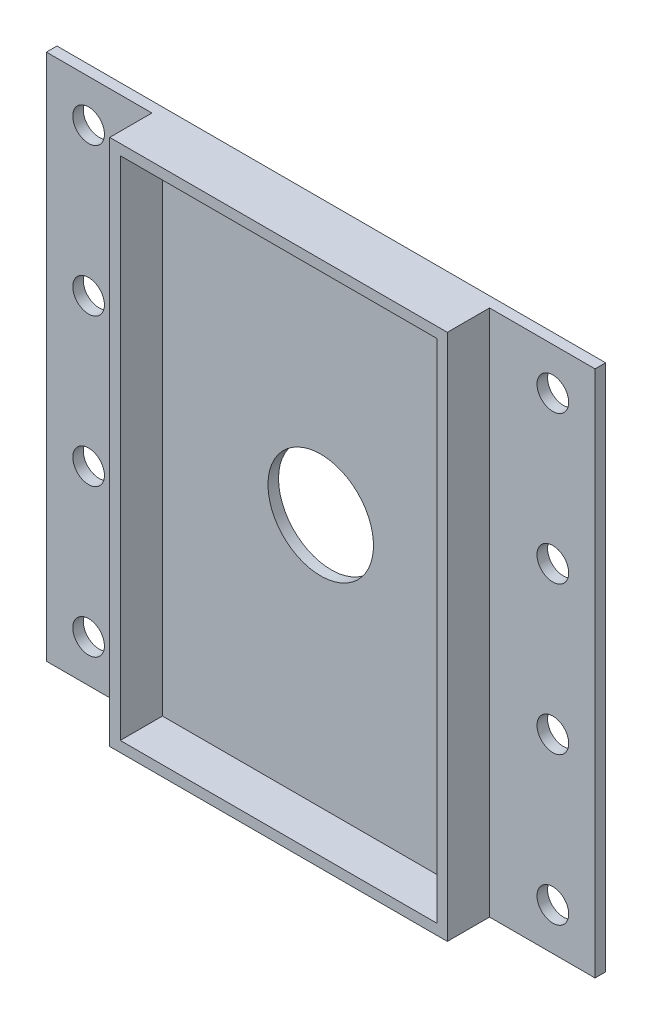
SolidWorks part; units mm, degrees
ref_plane "Plan de face" through (0, 0, 0) normal (0, 0, 1) x (1, 0, 0)
ref_plane "Plan de dessus" through (0, 0, 0) normal (0, 1, 0) x (1, 0, 0)
ref_plane "Plan de droite" through (0, 0, 0) normal (1, 0, 0) x (0, 0, -1)
sketch "Esquisse1" plane through (0, 0, 0) normal (0, 0, 1) x (1, 0, 0)
  line L0 (-5, 5) -> (-155, 5)
  line L1 (0, 0) -> (-160, 0)
  line L2 (0, 0) -> (0, 250)
  line L3 (0, 250) -> (-160, 250)
  line L4 (-160, 0) -> (-160, 250)
  line L5 (-155, 5) -> (-155, 245)
  line L6 (-5, 245) -> (-155, 245)
  line L7 (-5, 5) -> (-5, 245)
  dimension "D1" = 160
  dimension "D2" = 250
  dimension "D3" = 5
extrude "Boss.-Extru.1" add sketch "Esquisse1" along normal blind 20
sketch "Esquisse2" plane through (0, 0, 0) normal (0, 0, -1) x (-1, 0, 0)
  line L0 (155, 5) -> (5, 5) construction
  line L1 (-50, 250) -> (210, 250)
  line L2 (-50, 250) -> (-50, 0)
  line L3 (-50, 0) -> (210, 0)
  line L4 (210, 250) -> (210, 0)
  point P4 (80, 5)
  dimension "D1" = 260
  dimension "D2" = 130
extrude "Boss.-Extru.2" add sketch "Esquisse2" along normal blind 5
sketch "Esquisse3" plane through (0, 0, -5) normal (0, 0, -1) x (-1, 0, 0)
  line L0 (-50, 250) -> (210, 0) construction
  circle A0 centre (80, 125) radius 25
  dimension "D1" = 50
extrude "Enlèv. mat.-Extru.1" cut sketch "Esquisse3" against normal blind 5
sketch "Esquisse4" plane through (0, 0, 0) normal (0, 0, 1) x (1, 0, 0)
  line L0 (-210, 250) -> (-160, 250) construction
  line L1 (-210, 0) -> (-210, 250) construction
  line L2 (0, 250) -> (50, 250) construction
  line L4 (50, 250) -> (50, 0) construction
  circle A0 centre (30, 230) radius 7.5
  circle A1 centre (-190, 230) radius 7.5
  circle A2 centre (-190, 160) radius 7.5
  circle A3 centre (30, 160) radius 7.5
  circle A4 centre (-190, 90) radius 7.5
  circle A5 centre (30, 90) radius 7.5
  circle A6 centre (-190, 20) radius 7.5
  circle A7 centre (30, 20) radius 7.5
  point P4 (-185, 250)
  dimension "D6" = 15
  dimension "D7" = 15
  dimension "D1" = 20
  dimension "D2" = 20
  dimension "D3" = 20
  dimension "D4" = 20
  dimension "D5" = 4
extrude "Enlèv. mat.-Extru.2" cut sketch "Esquisse4" against normal blind 10
